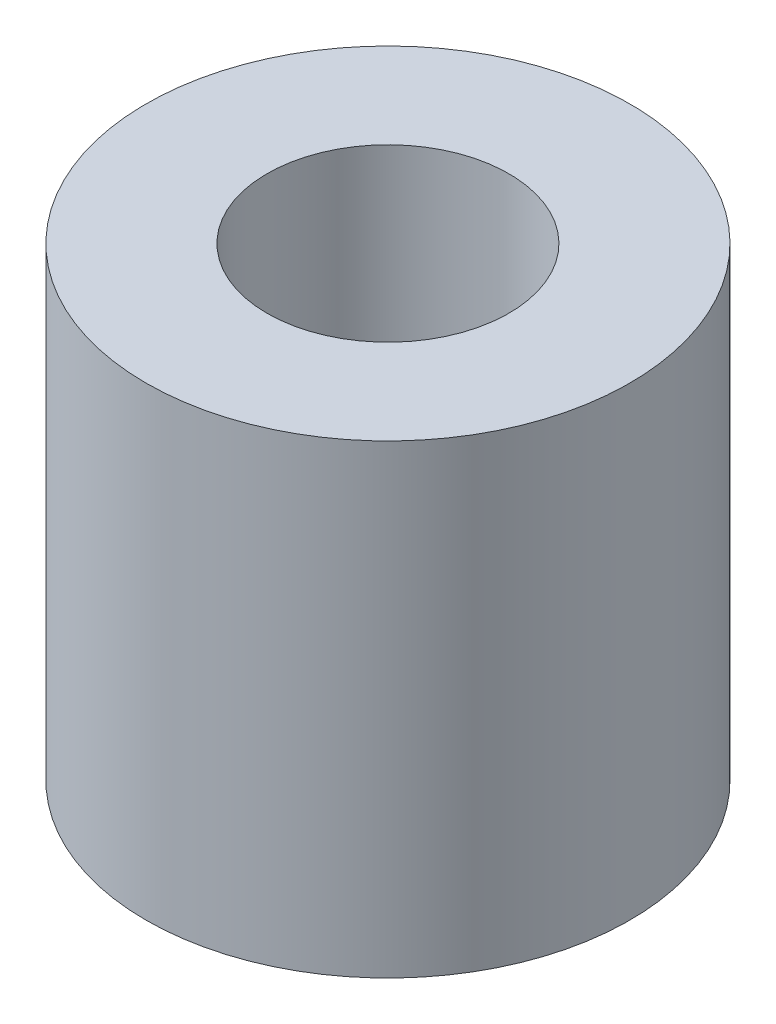
SolidWorks part; units mm, degrees
ref_plane "Front Plane" through (0, 0, 0) normal (0, 0, 1) x (1, 0, 0)
ref_plane "Top Plane" through (0, 0, 0) normal (0, 1, 0) x (1, 0, 0)
ref_plane "Right Plane" through (0, 0, 0) normal (1, 0, 0) x (0, 0, -1)
sketch "Sketch1" plane through (0, 0, 0) normal (0, 1, 0) x (1, 0, 0)
  circle A0 centre (0, 0) radius 3.302
  circle A1 centre (0, 0) radius 6.604
  dimension "D1" = 6.604
  dimension "D2" = 13.208
extrude "Boss-Extrude1" add sketch "Sketch1" along normal blind 12.7
